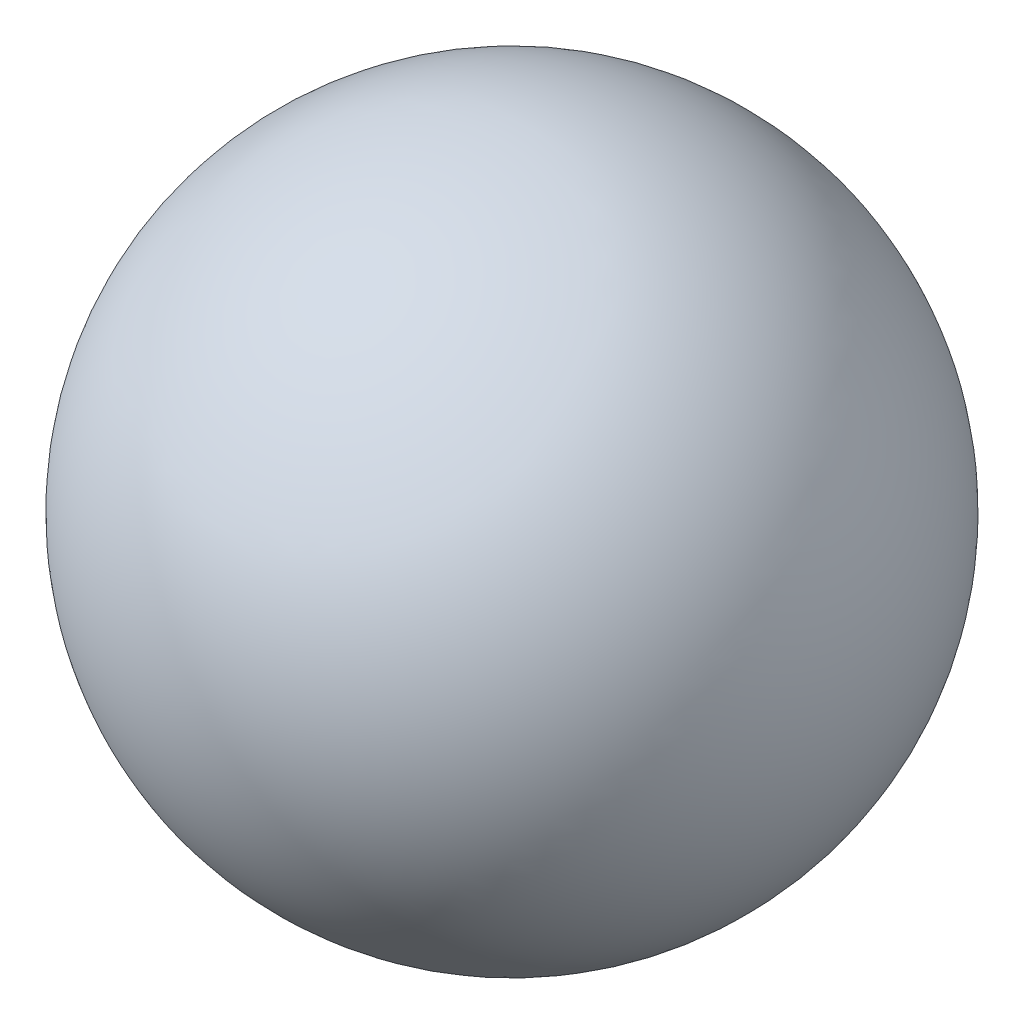
SolidWorks part; units mm, degrees
ref_plane "Front Plane" through (0, 0, 0) normal (0, 0, 1) x (1, 0, 0)
ref_plane "Top Plane" through (0, 0, 0) normal (0, 1, 0) x (1, 0, 0)
ref_plane "Right Plane" through (0, 0, 0) normal (1, 0, 0) x (0, 0, -1)
sketch "Sketch1" plane through (0, 0, 0) normal (0, 1, 0) x (1, 0, 0)
  line L0 (0, 11.1799) -> (0, -8.3849) construction
  circle A0 centre (0, 0) radius 6.35
  dimension "D1" = 12.7
revolve "Revolve4" add sketch "Sketch1" angle 360 about L0
